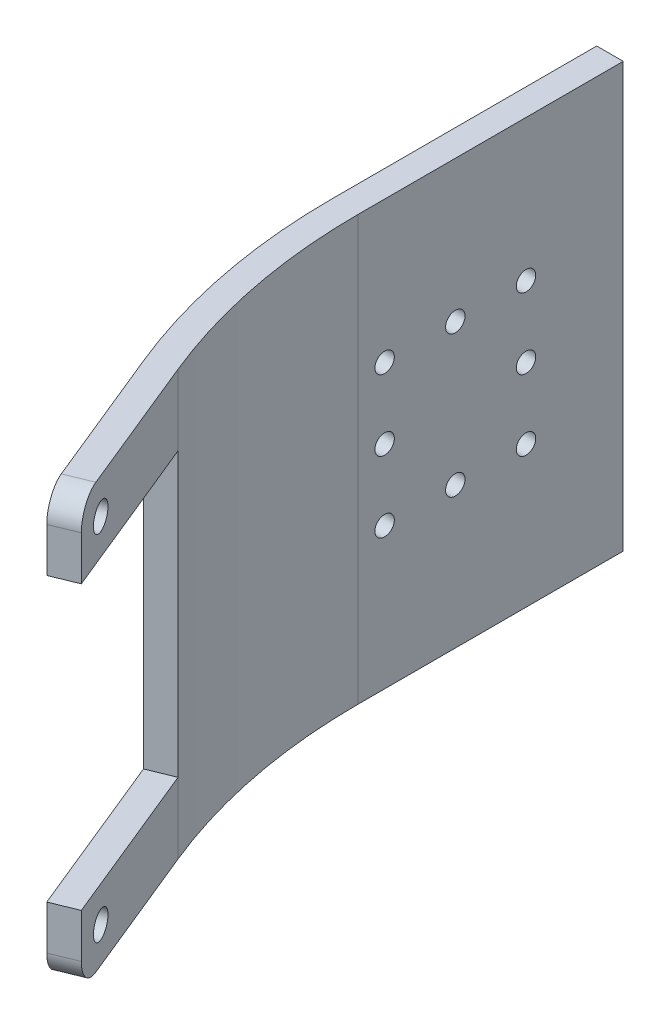
SolidWorks part; units mm, degrees
ref_plane "Face" through (0, 0, 0) normal (0, 0, 1) x (1, 0, 0)
ref_plane "Dessus" through (0, 0, 0) normal (0, 1, 0) x (1, 0, 0)
ref_plane "Droite" through (0, 0, 0) normal (1, 0, 0) x (0, 0, -1)
sketch "Esquisse1" plane through (0, 0, 0) normal (0, 1, 0) x (1, 0, 0)
  line L0 (0, 0) -> (0, 30)
  line L1 (0, 30) -> (3, 30)
  line L2 (3, 30) -> (3, 0)
  line L3 (5.2047, -26.487) -> (7.9816, -25.3519) construction
  line L4 (12.7724, -45) -> (15.5493, -43.8648)
  line L5 (5.2047, -26.487) -> (12.7724, -45)
  line L6 (7.9816, -25.3519) -> (15.5493, -43.8648)
  arc A0 (0, 0) -> (5.2047, -26.487) centre (70, 0) ccw
  arc A1 (3, 0) -> (7.9816, -25.3519) centre (70, 0) ccw
  dimension "D2" = 70
  dimension "D1" = 30
  dimension "D3" = 20
  dimension "D4" = 3
  dimension "D5" = 3
  dimension "D6" = 75
extrude "Extrusion1" add sketch "Esquisse1" along normal blind 48
sketch "Esquisse2" plane through (-4.8177, 0, 1.9694) normal (-0.9256, 0, 0.3784) x (0.3784, 0, 0.9256)
  line L0 (46.487, 24) -> (26.487, 24) construction
  line L1 (46.487, 48) -> (46.487, 0) construction
  line L2 (26.487, 48) -> (26.487, 0) construction
  line L3 (46.487, 40) -> (46.487, 8)
  line L4 (46.487, 8) -> (26.487, 8)
  line L5 (26.487, 8) -> (26.487, 40)
  line L6 (46.487, 40) -> (26.487, 40)
  line L7 (26.487, 0) -> (46.487, 0) construction
  line L8 (46.487, 24) -> (26.487, 24) construction
  line L9 (46.487, 48) -> (46.487, 0) construction
  line L10 (26.487, 48) -> (26.487, 0) construction
  circle A0 centre (42.487, 4) radius 1.5
  circle A1 centre (42.487, 44) radius 1.5
  point P10 (26.487, 24)
  dimension "D3" = 3
  dimension "D1" = 8
  dimension "D2" = 20
  dimension "D4" = 4
  dimension "D5" = 4
extrude "Extrusion3" cut sketch "Esquisse2" against normal up to next
fillet "Congé1" radius 3 2 edges at (14.1609, 0, 44.4324) (14.1609, 48, 44.4324)
sketch "Esquisse3" plane through (3, 0, 0) normal (1, 0, 0) x (0, 0, -1)
  line L0 (30, 24) -> (0, 24) construction
  line L1 (30, 48) -> (30, 0) construction
  line L2 (0, 48) -> (0, 0) construction
  line L3 (30, 16) -> (0, 16) construction
  line L4 (19, 24) -> (19, 0) construction
  line L5 (0, 0) -> (30, 0) construction
  line L6 (11, 24) -> (11, 0) construction
  line L7 (3, 24) -> (3, 0) construction
  circle A0 centre (3, 16) radius 1.1
  circle A1 centre (11, 16) radius 1.1
  circle A2 centre (19, 16) radius 1.1
  circle A3 centre (3, 24) radius 1.1
  circle A4 centre (19, 24) radius 1.1
  circle A5 centre (19, 32) radius 1.1
  circle A6 centre (11, 32) radius 1.1
  circle A7 centre (3, 32) radius 1.1
  dimension "D5" = 2.2
  dimension "D1" = 8
  dimension "D2" = 8
  dimension "D3" = 8
  dimension "D4" = 11
extrude "Extrusion4" cut sketch "Esquisse3" against normal up to next
